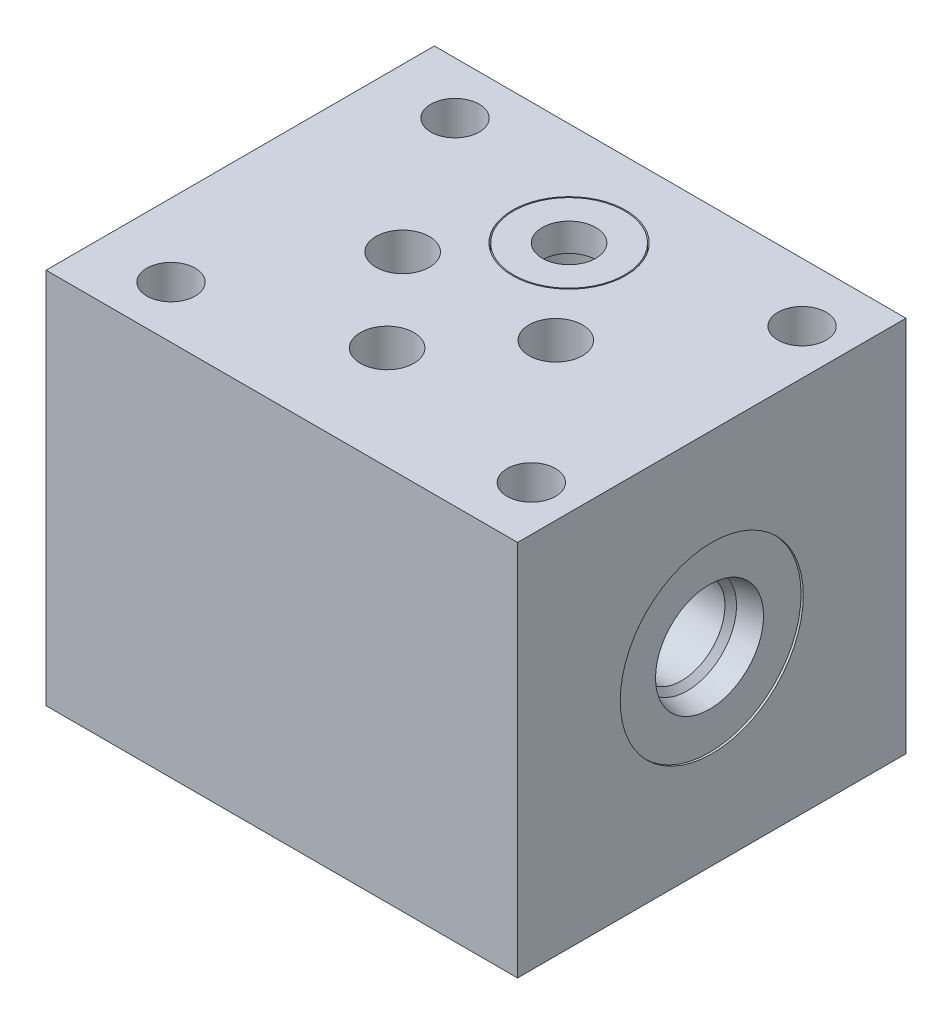
SolidWorks part; units mm, degrees
material "Alloy Steel"
ref_plane "Front Plane" through (0, 0, 0) normal (0, 0, 1) x (1, 0, 0)
ref_plane "Top Plane" through (0, 0, 0) normal (0, 1, 0) x (1, 0, 0)
ref_plane "Right Plane" through (0, 0, 0) normal (1, 0, 0) x (0, 0, -1)
ref_plane "Plane1" through (0, 0, 0) normal (0, 1, 0) x (1, 0, 0)
sketch "Sketch1" plane through (0, 0, 0) normal (0, 1, 0) x (1, 0, 0)
  line L0 (-26.9875, -22.225) -> (26.9875, -22.225)
  line L1 (26.9875, -22.225) -> (26.9875, 22.225)
  line L2 (26.9875, 22.225) -> (-26.9875, 22.225)
  line L3 (-26.9875, 22.225) -> (-26.9875, -22.225)
  line L4 (-29.6862, 0) -> (29.6862, 0) construction
  dimension "D1" = 44.45
  dimension "D2" = 53.975
  dimension "D3" = 26.9875
extrude "Extrude1" add sketch "Sketch1" along normal blind 43.18
sketch "Sketch2" plane through (0, 43.18, 0) normal (0, 1, 0) x (-1, 0, 0)
  circle A0 centre (-0.2413, 10.414) radius 3.0607
  circle A1 centre (-0.2413, -10.414) radius 3.0607
  circle A2 centre (-9.1313, 0) radius 3.0607
  circle A3 centre (8.3947, 0) radius 3.0607
  dimension "D1" = 6.1214
  dimension "D2" = 9.1313
  dimension "D3" = 10.414
  dimension "D4" = 8.3947
  dimension "D5" = 10.414
  dimension "D6" = 0.2413
  dimension "D7" = 0.2413
extrude "Cut-Extrude1" cut sketch "Sketch2" against normal through all
sketch "Sketch3" plane through (0, 0, 0) normal (0, -1, 0) x (1, 0, 0)
  circle A0 centre (0.2413, -10.414) radius 5.5626
  circle A1 centre (9.1313, 0) radius 5.5626
  circle A2 centre (0.2413, 10.414) radius 5.5626
  circle A3 centre (-8.3947, 0) radius 5.5626
  circle A4 centre (0.2413, -10.414) radius 3.0607 construction
  circle A5 centre (-8.3947, 0) radius 3.0607 construction
  circle A6 centre (0.2413, 10.414) radius 3.0607 construction
  circle A7 centre (9.1313, 0) radius 3.0607 construction
  dimension "D1" = 11.1252
extrude "Cut-Extrude2" cut sketch "Sketch3" against normal blind 1.27
ref_plane "Plane2" through (0.2413, 1.27, -10.414) normal (0, 0, 1) x (1, 0, 0)
sketch "Sketch4" plane through (0.2413, 1.27, -10.414) normal (0, 0, 1) x (1, 0, 0)
  line L0 (0, -1.8669) -> (0, 0.0889) construction
  line L2 (3.0607, 0) -> (3.0607, 41.91) construction
  line L3 (-3.0607, 41.91) -> (-3.0607, 0) construction
  line L5 (-5.5626, 0) -> (5.5626, 0) construction
  circle A0 centre (4.6736, -0.889) radius 0.889
  dimension "D1" = 1.778
  dimension "D2" = 9.3472
revolve "Revolve1" add sketch "Sketch4" angle 360 about L0
ref_plane "Plane3" through (9.1313, 1.27, 0) normal (0, 0, 1) x (1, 0, 0)
sketch "Sketch5" plane through (9.1313, 1.27, 0) normal (0, 0, 1) x (1, 0, 0)
  line L0 (0, -1.8669) -> (0, 0.0889) construction
  line L1 (-3.0607, 41.91) -> (-3.0607, 0) construction
  line L2 (3.0607, 0) -> (3.0607, 41.91) construction
  line L3 (-5.5626, 0) -> (5.5626, 0) construction
  circle A0 centre (4.6736, -0.889) radius 0.889
  dimension "D1" = 1.778
  dimension "D2" = 9.3472
revolve "Revolve2" add sketch "Sketch5" angle 360 about L0
ref_plane "Plane4" through (0.2413, 1.27, 10.414) normal (0, 0, 1) x (1, 0, 0)
sketch "Sketch6" plane through (0.2413, 1.27, 10.414) normal (0, 0, 1) x (1, 0, 0)
  line L0 (0, -1.8669) -> (0, 0.0889) construction
  line L1 (-3.0607, 41.91) -> (-3.0607, 0) construction
  line L2 (3.0607, 0) -> (3.0607, 41.91) construction
  line L3 (-5.5626, 0) -> (5.5626, 0) construction
  circle A0 centre (4.6736, -0.889) radius 0.889
  dimension "D1" = 1.778
  dimension "D2" = 9.3472
revolve "Revolve3" add sketch "Sketch6" angle 360 about L0
ref_plane "Plane5" through (-8.3947, 1.27, 0) normal (0, 0, 1) x (1, 0, 0)
sketch "Sketch7" plane through (-8.3947, 1.27, 0) normal (0, 0, 1) x (1, 0, 0)
  line L0 (0, -1.8669) -> (0, 0.0889) construction
  line L1 (3.0607, 0) -> (3.0607, 41.91) construction
  line L2 (-3.0607, 41.91) -> (-3.0607, 0) construction
  line L3 (-3.0607, 0) -> (3.0607, 0) construction
  circle A0 centre (4.6736, -0.889) radius 0.889
  dimension "D1" = 1.778
  dimension "D2" = 9.3472
revolve "Revolve4" add sketch "Sketch7" angle 360 about L0
ref_plane "Plane6" through (26.9875, 21.59, 0) normal (0, 0, 1) x (0, -1, 0)
sketch "S2D0007" plane through (26.9875, 21.59, 0) normal (0, 0, 1) x (0, -1, 0)
  line L0 (0, 0) -> (10.4775, 0)
  line L1 (10.4775, 0) -> (10.4775, -0.254)
  line L2 (10.4775, -0.254) -> (6.1849, -0.254)
  line L3 (6.1849, -0.254) -> (5.6423, -2.8067)
  line L4 (5.6423, -2.8067) -> (4.9784, -3.4706)
  line L5 (4.9784, -3.4706) -> (4.9784, -14.224)
  line L6 (4.9784, -14.224) -> (0, -14.224)
  line L7 (0, -14.224) -> (0, 0)
  line L8 (0, -21.9267) -> (0, 0.7112) construction
  line L9 (-21.59, -53.975) -> (-21.59, 0) construction
  line L10 (-21.59, 0) -> (21.59, 0) construction
  dimension "D1" = 0.254
  dimension "D2" = 21.59
  dimension "D3" = 20.955
  dimension "D4" = 12.3698
  dimension "D5" = 13.97
  dimension "D6" = 9.9568
  dimension "D7" = 45
  dimension "D8" = 2.5527
  dimension "D9" = 12
revolve "Cut-Revolve1" cut sketch "S2D0007" angle 360 about L8
ref_plane "Plane7" through (-26.9875, 21.59, 0) normal (0, 0, 1) x (0, 1, 0)
sketch "Sketch9" plane through (-26.9875, 21.59, 0) normal (0, 0, 1) x (0, 1, 0)
  line L0 (0, 0) -> (10.4775, 0)
  line L1 (10.4775, 0) -> (10.4775, -0.254)
  line L2 (10.4775, -0.254) -> (6.1849, -0.254)
  line L3 (6.1849, -0.254) -> (5.6423, -2.8067)
  line L4 (5.6423, -2.8067) -> (4.9784, -3.4706)
  line L5 (4.9784, -3.4706) -> (4.9784, -14.224)
  line L6 (4.9784, -14.224) -> (0, -14.224)
  line L7 (0, -14.224) -> (0, 0)
  line L8 (0, -14.9352) -> (0, 0.7112) construction
  line L9 (21.59, 0) -> (21.59, -53.975) construction
  line L10 (21.59, 0) -> (-21.59, 0) construction
  dimension "D1" = 0.254
  dimension "D2" = 21.59
  dimension "D3" = 9.9568
  dimension "D4" = 13.97
  dimension "D5" = 20.955
  dimension "D6" = 12.3698
  dimension "D7" = 12
  dimension "D8" = 45
  dimension "D9" = 2.5527
revolve "Cut-Revolve2" cut sketch "Sketch9" angle 360 about L8
ref_plane "Plane8" through (26.9875, 21.59, 0) normal (0, 0, 1) x (0, -1, 0)
sketch "S2D0006" plane through (26.9875, 21.59, 0) normal (0, 0, 1) x (0, -1, 0)
  line L0 (0, 0) -> (2.1844, 0)
  line L1 (2.1844, 0) -> (2.1844, -17.8562)
  line L2 (2.1844, -17.8562) -> (0, -19.1687)
  line L3 (0, -19.1687) -> (0, 0)
  line L4 (0, -20.1272) -> (0, 0.9584) construction
  line L5 (-4.9784, -3.4706) -> (-4.9784, -14.224) construction
  line L6 (4.9784, -14.224) -> (4.9784, -3.4706) construction
  line L7 (-21.59, 0) -> (21.59, 0) construction
  dimension "D1" = 4.3688
  dimension "D2" = 59
  dimension "D3" = 17.8562
revolve "Cut-Revolve3" cut sketch "S2D0006" angle 360 about L4
ref_plane "Plane9" through (-26.9875, 21.59, 0) normal (0, 0, 1) x (0, 1, 0)
sketch "Sketch11" plane through (-26.9875, 21.59, 0) normal (0, 0, 1) x (0, 1, 0)
  line L0 (0, 0) -> (2.1844, 0)
  line L1 (2.1844, 0) -> (2.1844, -15.4178)
  line L2 (2.1844, -15.4178) -> (0, -16.7303)
  line L3 (0, -16.7303) -> (0, 0)
  line L4 (0, -17.5668) -> (0, 0.8365) construction
  line L5 (4.9784, -14.224) -> (4.9784, -3.4706) construction
  line L6 (-4.9784, -3.4706) -> (-4.9784, -14.224) construction
  line L7 (21.59, 0) -> (-21.59, 0) construction
  dimension "D1" = 4.3688
  dimension "D2" = 59
  dimension "D3" = 15.4178
revolve "Cut-Revolve4" cut sketch "Sketch11" angle 360 about L4
ref_plane "Plane10" through (0.2413, 1.27, -10.414) normal (0, 0, 1) x (1, 0, 0)
sketch "Sketch16" plane through (0, 43.18, 0) normal (0, 1, 0) x (1, 0, 0)
  circle A0 centre (0.2413, 10.414) radius 6.4897
  dimension "D1" = 12.9794
extrude "Cut-Extrude3" cut sketch "Sketch16" against normal blind 3.2004
sketch "Sketch17" plane through (0, 43.18, 0) normal (0, 1, 0) x (1, 0, 0)
  circle A0 centre (0.2413, 10.414) radius 5.7785
  dimension "D1" = 11.557
extrude "Cut-Extrude4" cut sketch "Sketch17" against normal blind 17.6784
sketch "Sketch12" plane through (0.2413, 1.27, -10.414) normal (0, 0, 1) x (1, 0, 0)
  line L0 (0, 22.6416) -> (0, 33.1191) construction
  line L1 (0, 23.1179) -> (0, 32.6429)
  arc A0 (0, 23.1179) -> (0, 32.6429) centre (0, 27.8804) ccw
  point P0 (3.0607, 24.2316)
  dimension "D1" = 4.7625
revolve "Revolve5" add sketch "Sketch12" angle 360 about L0
sketch "Sketch13" plane through (0, 43.18, 0) normal (0, 1, 0) x (-1, 0, 0)
  circle A0 centre (-0.2413, -10.414) radius 6.35
  circle A1 centre (-0.2413, -10.414) radius 3.0607
ref_plane "Plane11" through (0.2413, 39.9796, -10.414) normal (0, -1, 0) x (1, 0, 0)
extrude "Extrude2" add sketch "Sketch13" against normal up to surface (3.2004 mm away) up to plane "Plane11"
hole_wizard "Hole1" positions "Sketch19" profile "Sketch18" legacy end condition through all
sketch "Sketch19" plane through (0, 0, 0) normal (0, -1, 0) x (1, 0, 0)
  line L0 (26.9875, 22.225) -> (26.9875, -22.225) construction
  line L1 (-26.9875, 22.225) -> (26.9875, 22.225) construction
  point P0 (21.8313, 15.494)
  point P1 (-18.6563, 16.256)
  point P3 (-18.6563, -16.256)
  point P5 (21.8313, -15.494)
  dimension "D1" = 5.1562
  dimension "D2" = 6.731
  dimension "D3" = 30.988
  dimension "D4" = 40.4876
  dimension "D5" = 0.762
  dimension "D6" = 31.75
sketch "Sketch18" plane through (21.8313, 0, 15.494) normal (1, 0, 0) x (0, 0, -1)
  line L0 (0, 0) -> (0, 43.18)
  line L1 (0, 43.18) -> (2.7686, 43.18)
  line L2 (2.7686, 43.18) -> (2.7686, 0)
  line L3 (2.7686, 0) -> (0, 0)
  line L4 (0, 110) -> (0, -10) construction
  dimension "Diameter" = 5.5372
  dimension "Depth" = 43.18
